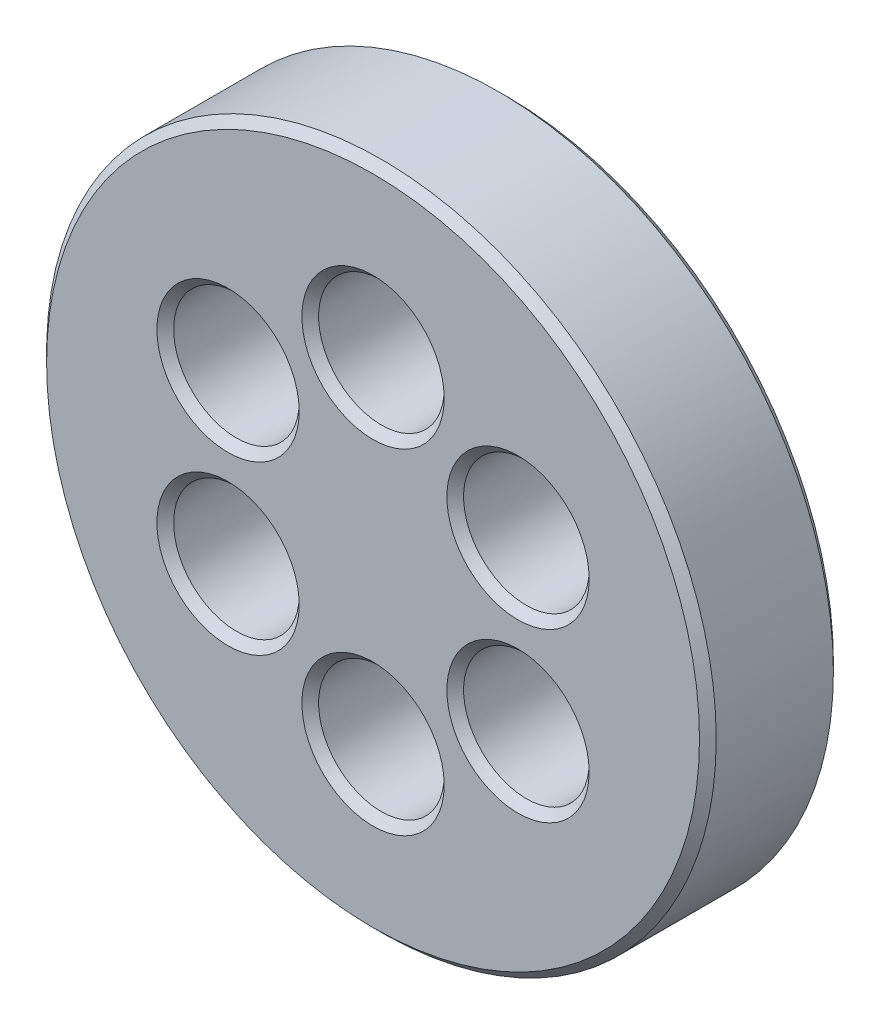
SolidWorks part; units mm, degrees
ref_plane "Front Plane" through (0, 0, 0) normal (0, 0, 1) x (1, 0, 0)
ref_plane "Top Plane" through (0, 0, 0) normal (0, 1, 0) x (1, 0, 0)
ref_plane "Right Plane" through (0, 0, 0) normal (1, 0, 0) x (0, 0, -1)
sketch "Sketch3" plane through (0, 0, 0) normal (0, 0, 1) x (1, 0, 0)
  circle A0 centre (0, 0) radius 20
  dimension "D2" = 40
extrude "Boss-Extrude1" add sketch "Sketch3" along normal blind 8
sketch "Sketch4" plane through (0, 0, 8) normal (0, 0, 1) x (1, 0, 0)
  circle A1 centre (0, 0) radius 10 construction
  circle A2 centre (0, 10) radius 3.75
  dimension "D1" = 20
  dimension "D2" = 7.5
extrude "Cut-Extrude1" cut sketch "Sketch4" against normal blind 8
pattern_circular "CirPattern1" count 6 over 360 about axis through (0, 0, 0) along (0, 0, 1) of "Cut-Extrude1"
chamfer "Chamfer1" distance 0.5 14 edges at (-10.5353, -1.7524, 8) (-10.5353, -1.7524, 0) (-3.75, -10, 8) (-3.75, -10, 0) (6.7853, -8.2476, 8) (6.7853, -8.2476, 0) (10.5353, 1.7524, 8) (10.5353, 1.7524, 0) (3.75, 10, 8) (3.75, 10, 0) (-6.7853, 8.2476, 8) (-6.7853, 8.2476, 0) (20, 0, 0) (20, 0, 8)
